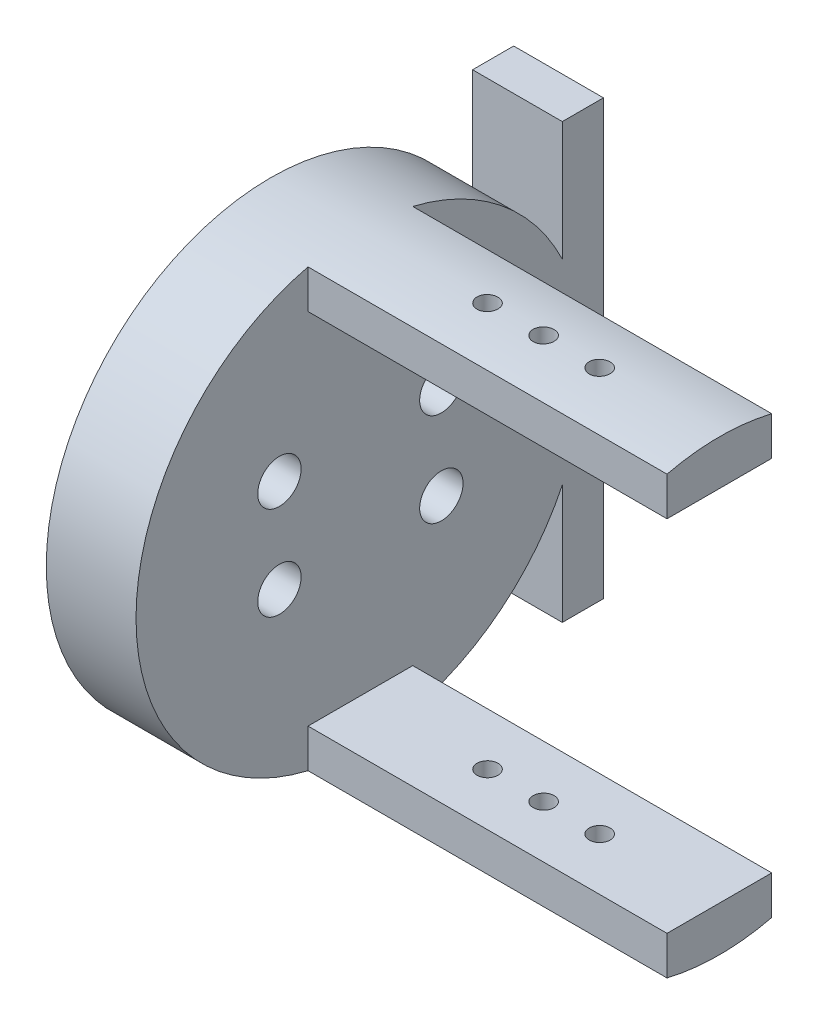
SolidWorks part; units mm, degrees
other "标注1"
sketch "草图20" plane through (-40, 128, 27.5) normal (-0.9349, 0.1755, 0.3084) x (0.3368, 0.1651, 0.927)
ref_plane "前视基准面" through (0, 0, 0) normal (0, 0, 1) x (1, 0, 0)
ref_plane "上视基准面" through (0, 0, 0) normal (0, 1, 0) x (1, 0, 0)
ref_plane "右视基准面" through (0, 0, 0) normal (1, 0, 0) x (0, 0, -1)
other "Configuration Table"
ref_plane "基准面6" through (10, 0, 0) normal (1, 0, 0) x (0, 0, -1)
sketch "草图23" plane through (10, 0, 0) normal (1, 0, 0) x (0, 0, -1)
  line L1 (32.5, 0) -> (32.5, 29)
  line L2 (32.5, 29) -> (27, 29)
  line L3 (27, 29) -> (27, 13.0767)
  line L5 (32.5, 0) -> (32.5, -29)
  line L6 (32.5, -29) -> (27, -29)
  line L7 (27, -29) -> (27, -13.0767)
  arc A0 (27, 13.0767) -> (27, -13.0767) centre (0, 0) ccw
  circle A1 centre (0, 12.5) radius 1.6
  circle A2 centre (-10.8253, 6.25) radius 1.6
  circle A3 centre (10.8253, 6.25) radius 1.6
  circle A4 centre (10.8253, -6.25) radius 1.6
  circle A5 centre (0, -12.5) radius 1.6
  circle A6 centre (-10.8253, -6.25) radius 1.6
  circle A7 centre (5.1, 8.8335) radius 2.15
  circle A8 centre (-10.2, 0) radius 2.15
  circle A9 centre (5.1, -8.8335) radius 2.15
extrude "凸台-拉伸9" add sketch "草图23" against normal blind 12 separate body
sketch "草图25" plane through (10, 0, 0) normal (1, 0, 0) x (0, 0, -1)
  circle A0 centre (5.1, 8.8335) radius 3.1995
  circle A1 centre (-10.2, 0) radius 3.2536
  circle A2 centre (5.1, -8.8335) radius 3.504
extrude "凸台-拉伸11" add sketch "草图25" against normal blind 8.5
sketch "草图27" plane through (10, 0, 0) normal (1, 0, 0) x (0, 0, -1)
  circle A0 centre (0, 12.5) radius 2.9
  circle A1 centre (-86.6597, 123.7299) radius 2.9
  circle A2 centre (-33.6616, 254.3944) radius 2.9
  circle A3 centre (105.9962, 273.8289) radius 2.9
  circle A4 centre (192.6559, 162.599) radius 2.9
  circle A5 centre (139.6578, 31.9345) radius 2.9
  circle A6 centre (10.8253, 6.25) radius 2.9
  circle A7 centre (10.8253, -6.25) radius 2.9
  circle A8 centre (0, -12.5) radius 2.9
  circle A9 centre (-10.8253, -6.25) radius 2.9
  circle A10 centre (-10.8253, 6.25) radius 2.9
  point P16 (52.9981, 143.1645)
  point P26 (0, 0)
  dimension "D1" = 6
  dimension "D2" = 6
extrude "切除-拉伸14" cut sketch "草图27" against normal blind 5 and the other way blind 15
sketch "草图29" plane through (10, 0, 0) normal (1, 0, 0) x (0, 0, -1)
  line L3 (-7, 29.1719) -> (-7, -29.1719)
  line L5 (7, -29.1719) -> (7, 29.1719)
  arc A1 (7, 29.1719) -> (-7, 29.1719) centre (0, 0) ccw
  arc A2 (-7, -29.1719) -> (7, -29.1719) centre (0, 0) ccw
extrude "凸台-拉伸14" add sketch "草图29" along normal blind 48 and the other way blind 8.5 contours L3 A2 L5 A1
sketch "草图30" plane through (-2, 0, 0) normal (-1, 0, 0) x (0, 0, 1)
  circle A0 centre (0, 12.5) radius 2.8231
  circle A1 centre (0, -12.5) radius 3.0998
extrude "凸台-拉伸15" add sketch "草图30" against normal up to next
sketch "草图32" plane through (0, 0, -7) normal (0, 0, -1) x (-1, 0, 0)
  line L0 (-58, 0) -> (-58, 24)
  line L1 (-58, -29.1719) -> (-58, 29.1719) construction
  line L2 (-58, 0) -> (-58, -24)
  line L3 (-58, 24) -> (-10, 24)
  line L4 (-10, 55) -> (-10, -55) construction
  line L5 (-10, 24) -> (-10, -24)
  line L6 (-10, -24) -> (-58, -24)
extrude "切除-拉伸15" cut sketch "草图32" against normal through all
sketch "草图33" plane through (0, -24, 0) normal (0, 1, 0) x (1, 0, 0)
  circle A0 centre (34.5, 0) radius 1.4
  circle A1 centre (42, 0) radius 1.4
  circle A2 centre (27, 0) radius 1.4
  point P5 (42, 0.122)
extrude "切除-拉伸16" cut sketch "草图33" against normal up to next and the other way up to next
